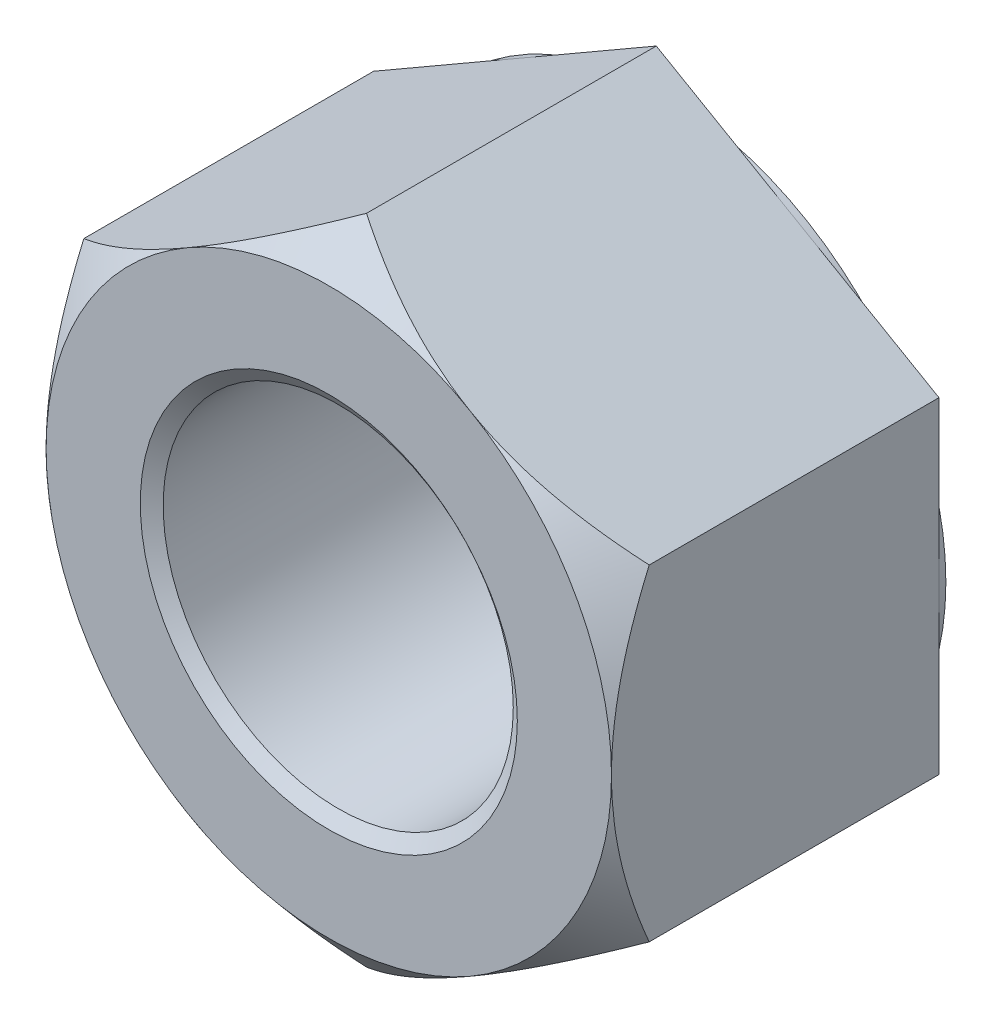
SolidWorks part; units mm, degrees
extrude "BaseNut" add sketch "BaseNutSke" against normal blind 19.7104
sketch "BaseNutSke" plane through (0, 0, 0) normal (0, 0, 1) x (1, 0, 0)
  line L6 (16.6624, 9.62) -> (16.6624, -9.62)
  line L7 (-16.6624, 9.62) -> (-16.6624, -9.62)
  line L8 (16.6624, 9.62) -> (0, 19.2401)
  line L9 (0, 19.2401) -> (-16.6624, 9.62)
  line L10 (-16.6624, -9.62) -> (0, -19.2401)
  line L11 (0, -19.2401) -> (16.6624, -9.62)
  circle A0 centre (0, 0) radius 10.3187
  dimension "Tap_drill" = 20.6375
  dimension "Width_flats" = 33.3248
  dimension "D2" = 16.6624
  dimension "D3" = 16.6624
  dimension "D1" = 120
  dimension "D4" = 16.6624
cosmetic thread "ThreadCosmetic" parameters "Thread_major"=22.225
pattern_linear "ThdSchPat" [suppressed]
revolve "ThreadSchematic" [suppressed] cut sketch "ThdSchSke" angle 360 about L6
sketch "ThdSchSke" plane through (0, 0, 0) normal (0, 1, 0) x (1, 0, 0)
  line L0 (-11.1125, 0.0254) -> (-10.3187, 0.5812)
  line L1 (-10.3187, 0.5812) -> (-5.1594, 0.5812)
  line L2 (-5.1594, 0.5812) -> (-5.1594, -0.5304)
  line L3 (-5.1594, -0.5304) -> (-10.3187, -0.5304)
  line L4 (-10.3187, -0.5304) -> (-11.1125, 0.0254)
  line L5 (-3.175, 1.8136) -> (3.175, 1.8136) construction
  line L6 (0, 1.8136) -> (0, -2.9874) construction
  line L7 (0, 19.1292) -> (0, 0.5558) construction
  dimension "Thread_major" = 22.225
  dimension "SideAngle" = 55
  dimension "Advance" = 1.8136
  dimension "D1" = 0.0254
material "AISI Type 316L stainless steel"
ref_plane "Plane1" through (0, 0, 0) normal (0, 0, 1) x (1, 0, 0)
ref_plane "Plane2" through (0, 0, 0) normal (0, 1, 0) x (1, 0, 0)
ref_plane "Plane3" through (0, 0, 0) normal (1, 0, 0) x (0, 0, -1)
sketch "Sketch4" plane through (0, 0, 0) normal (1, 0, 0) x (0, 0, -1)
  line L0 (19.7104, 16.6624) -> (19.304, 16.6624)
  line L1 (19.7104, 16.6624) -> (19.7104, 31.9401)
  line L2 (19.304, 31.9401) -> (19.7104, 31.9401)
  line L3 (19.304, 31.9401) -> (19.304, 16.6624)
  line L4 (0, 0) -> (34.925, 0) construction
  line L6 (19.7104, 9.62) -> (19.7104, 19.2401) construction
  line L7 (0, 16.6624) -> (-12.7, 16.6624)
  line L8 (0, 9.62) -> (0, 19.2401) construction
  line L9 (2.2225, 19.2401) -> (2.2225, 31.9401)
  line L10 (2.2225, 31.9401) -> (-12.7, 31.9401)
  line L11 (-12.7, 31.9401) -> (-12.7, 16.6624)
  line L12 (0, 16.6624) -> (2.2225, 19.2401)
  line L14 (0, 9.62) -> (0, -9.62) construction
  line L15 (19.7104, 19.2401) -> (0, 19.2401) construction
  dimension "D1" = 16.6624
  dimension "D2" = 2.2225
  dimension "D3" = 12.7
  dimension "D4" = 12.7
revolve "Bearing-Face" cut sketch "Sketch4" angle 360 about L4
sketch "Sketch3" plane through (0, 0, 0) normal (1, 0, 0) x (0, 0, -1)
  line L0 (19.7104, 16.6624) -> (17.4879, 19.2401)
  line L1 (17.4879, 19.2401) -> (17.4879, 31.9401)
  line L2 (17.4879, 31.9401) -> (32.4104, 31.9401)
  line L3 (32.4104, 31.9401) -> (32.4104, 16.6624)
  line L4 (32.4104, 16.6624) -> (19.7104, 16.6624)
  line L5 (19.7104, 9.62) -> (19.7104, 19.2401) construction
  line L6 (19.304, 19.2401) -> (2.2225, 19.2401) construction
  line L7 (0, 0) -> (38.6776, 0) construction
  line L8 (19.7104, 0) -> (0, 0) construction
  line L9 (10.7632, 19.2401) -> (10.7632, 44.222) construction
  line L10 (4.0386, 31.9401) -> (-10.8839, 31.9401)
  line L11 (-10.8839, 31.9401) -> (-10.8839, 16.6624)
  line L12 (-10.8839, 16.6624) -> (1.8161, 16.6624)
  line L13 (1.8161, 16.6624) -> (4.0386, 19.2401)
  line L14 (4.0386, 19.2401) -> (4.0386, 31.9401)
  line L16 (19.304, 19.2401) -> (2.2225, 19.2401) construction
  dimension "D1" = 16.6624
  dimension "D2" = 2.2225
  dimension "D4" = 12.7
  dimension "D3" = 12.7
revolve "Double-Chamfer" [suppressed] cut sketch "Sketch3" angle 360 about L7
sketch "Sketch5" plane through (0, 0, 0) normal (1, 0, 0) x (0, 0, -1)
  line L0 (19.685, 11.1125) -> (19.0736, 10.2394)
  line L1 (19.7358, 11.1125) -> (19.685, 11.1125)
  line L2 (19.7358, 11.1125) -> (19.7358, 10.2394)
  line L3 (19.7358, 10.2394) -> (19.0736, 10.2394)
  line L6 (-0.0508, 11.1125) -> (0, 11.1125)
  line L7 (0, 11.1125) -> (0.6114, 10.2394)
  line L9 (0.6114, 10.2394) -> (-0.0508, 10.2394)
  line L10 (-0.0508, 10.2394) -> (-0.0508, 11.1125)
  line L11 (25.0375, 0) -> (38.388, 0) construction
  line L12 (19.7104, 0) -> (0, 0) construction
  dimension "D1" = 35
  dimension "D2" = 0.0508
  dimension "ThreadMajor" = 11.1125
  dimension "Offset1" = 19.7358
revolve "EndChamfer" cut sketch "Sketch5" angle 360 about L11
equation "\"D2@BaseNutSke\" = \"Width_flats@BaseNutSke\" / 2"
equation "\"D3@BaseNutSke\" = \"Width_flats@BaseNutSke\" / 2"
equation "\"D1@Sketch3\" = \"Width_flats@BaseNutSke\" /2"
equation "\"D2@Sketch3\" = \"Thread_major@ThreadCosmetic\" *.1"
equation "\"D1@Sketch4\" = \"D2@BaseNutSke\""
equation "\"D2@Sketch4\" = \"Thread_major@ThreadCosmetic\" *.10"
equation "\"D4@BaseNutSke\" = \"D3@BaseNutSke\""
equation "\"Thread_major@ThdSchSke\" = \"Thread_major@ThreadCosmetic\""
equation "\"Tap_Drill@ThdSchSke\" = \"Tap_drill@BaseNutSke\""
equation "\"OverCut@ThdSchSke\" = \"Tap_Drill@ThdSchSke\" * 0.5"
equation "\"Num_threads@ThdSchPat\" = int(  ( \"Thickness@BaseNut\" - 0.002 ) / \"Advance@ThdSchSke\" + 0.999 )  + 1"
equation "\"Advance@ThdSchPat\" = ( \"Thickness@BaseNut\" - 0.002 ) /  (\"Num_threads@ThdSchPat\" - 1) 'relax it"
equation "' \"Num_threads@ThdSchPat\" = \"Num_threads@ThdSchPat\" - sgn( \"Num_threads@ThdSchPat\" - 1) '---chamfered tips only---"
equation "\"ThreadMajor@Sketch5\" = \"Thread_major@ThreadCosmetic\" * 0.5"
equation "\"ChamferDepth@Sketch5\" = (\"Thread_major@ThreadCosmetic\" - \"Tap_drill@BaseNutSke\") * 0.55"
equation "\"Offset1@Sketch5\" = \"Thickness@BaseNut\" + 0.001"
equation "\"Offset2@Sketch5\" = \"Offset1@Sketch5\" + 0.002"
